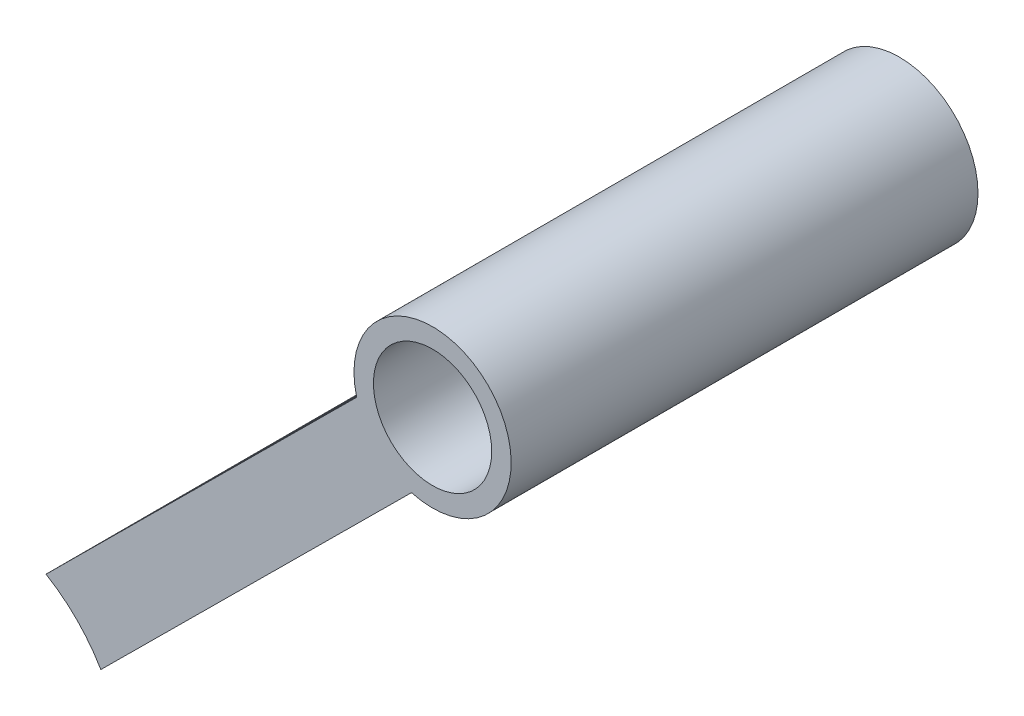
SolidWorks part; units mm, degrees
ref_plane "Front" through (0, 0, 0) normal (0, 0, 1) x (1, 0, 0)
ref_plane "Top" through (0, 0, 0) normal (0, 1, 0) x (1, 0, 0)
ref_plane "Right" through (0, 0, 0) normal (1, 0, 0) x (0, 0, -1)
sketch "Sketch2" plane through (0, 0, -31.75) normal (0, 0, 1) x (1, 0, 0)
  circle A0 centre (38.0356, 37.7748) radius 6.4135
  circle A1 centre (38.0356, 37.7748) radius 4.826
  circle A3 centre (38.0356, 37.7748) radius 4.826 construction
  dimension "D1" = 1.5875
extrude "Extrude1" add sketch "Sketch2" along normal blind 38.1
sketch "Sketch3" plane through (0, 0, 6.35) normal (0, 0, 1) x (1, 0, 0)
  line L0 (31.8444, 36.1009) -> (6.4876, 10.9179)
  line L1 (36.3191, 31.5953) -> (10.9623, 6.4124)
  line L2 (38.0356, 37.7748) -> (0, 0) construction
  circle A0 centre (38.0356, 37.7748) radius 6.4135 construction
  circle A1 centre (0, 0) radius 12.7 construction
  circle A2 centre (0, 0) radius 11.1125 construction
  arc A3 (6.4876, 10.9179) -> (10.9623, 6.4124) centre (0, 0) cw
  arc A4 (31.8444, 36.1009) -> (36.3191, 31.5953) centre (38.0356, 37.7748) ccw
  dimension "D1" = 6.35
extrude "Extrude2" add sketch "Sketch3" against normal blind 25.4
